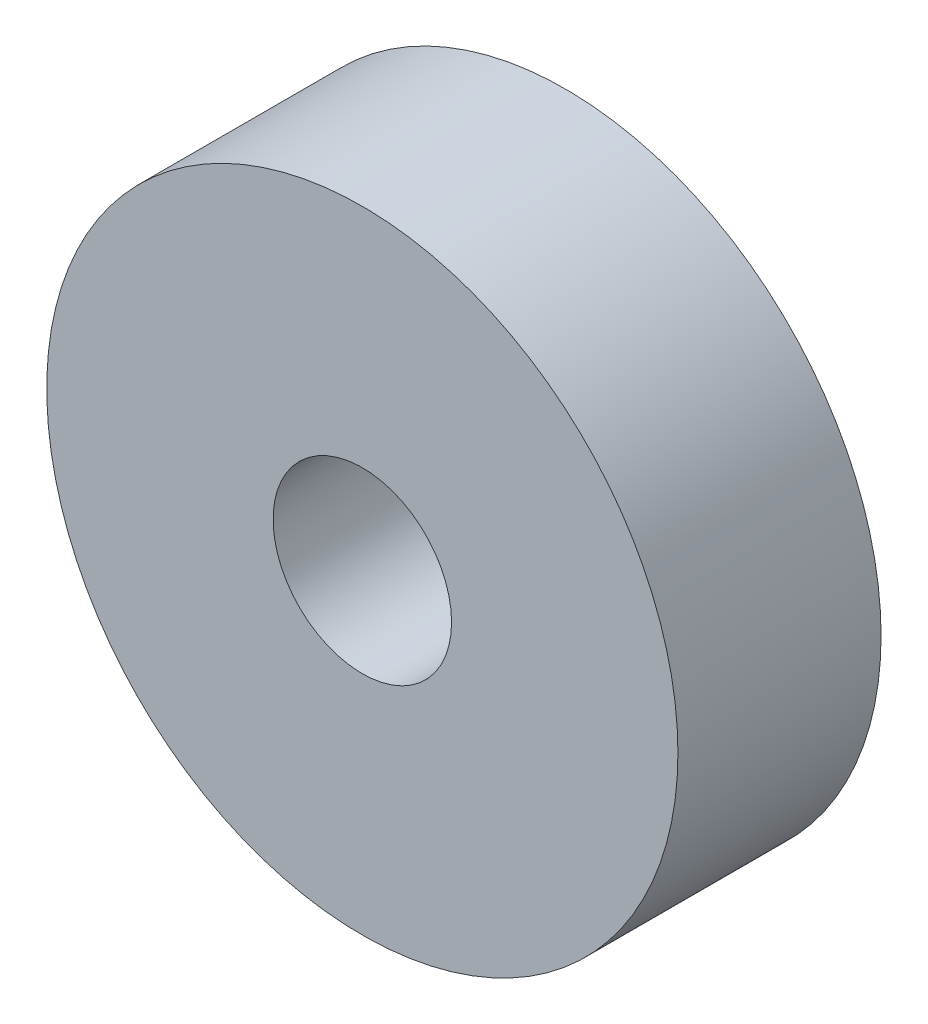
SolidWorks part; units mm, degrees
ref_plane "Front Plane" through (0, 0, 0) normal (0, 0, 1) x (1, 0, 0)
ref_plane "Top Plane" through (0, 0, 0) normal (0, 1, 0) x (1, 0, 0)
ref_plane "Right Plane" through (0, 0, 0) normal (1, 0, 0) x (0, 0, -1)
sketch "Sketch1" plane through (0, 0, 0) normal (0, 0, 1) x (1, 0, 0)
  circle A0 centre (0, 0) radius 10.875
  circle A1 centre (0, 0) radius 3.075
  dimension "D1" = 6.15
  dimension "D2" = 21.75
extrude "Boss-Extrude1" add sketch "Sketch1" along normal blind 7
